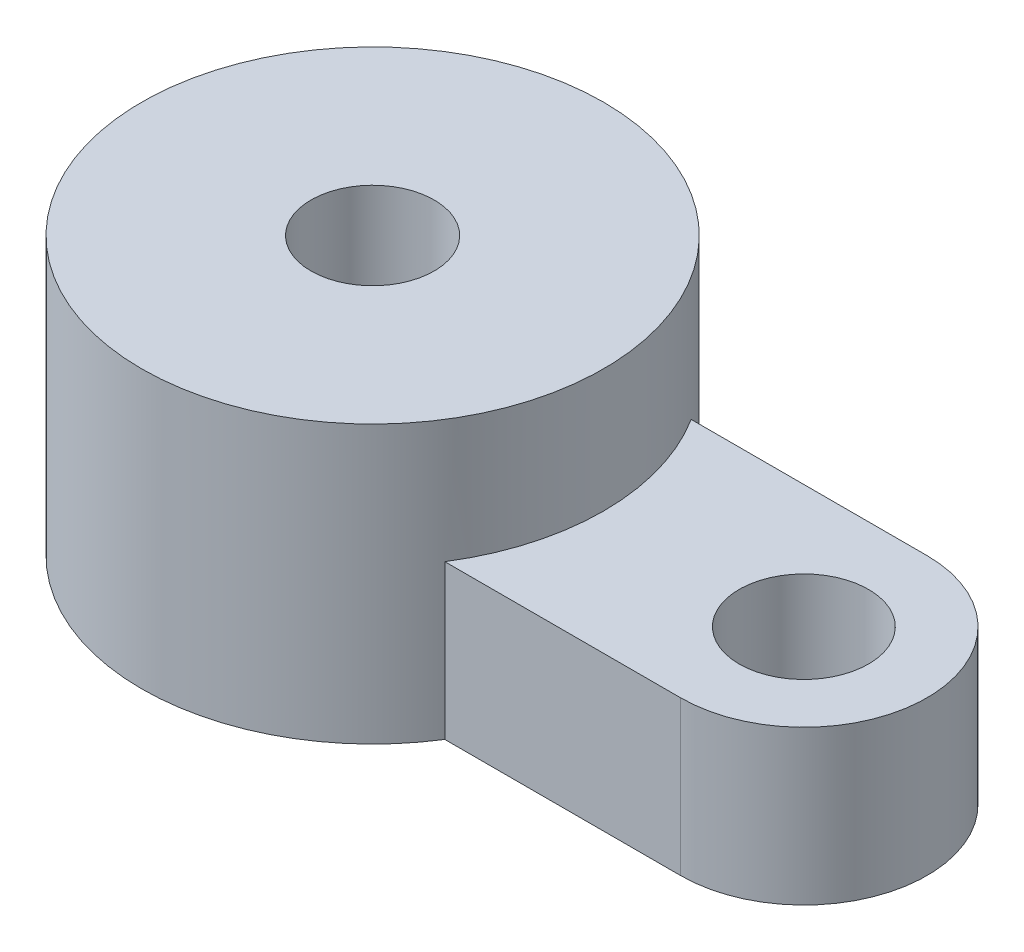
SolidWorks part; units mm, degrees
ref_plane "前视基准面" through (0, 0, 0) normal (0, 0, 1) x (1, 0, 0)
ref_plane "上视基准面" through (0, 0, 0) normal (0, 1, 0) x (1, 0, 0)
ref_plane "右视基准面" through (0, 0, 0) normal (1, 0, 0) x (0, 0, -1)
sketch "草图1" plane through (0, 0, 0) normal (0, 1, 0) x (1, 0, 0)
  line L0 (0, 0) -> (14.003, 0) construction
  line L1 (0, 4) -> (14.003, 4)
  line L2 (0, -4) -> (14.003, -4)
  arc A0 (0, 4) -> (0, -4) centre (0, 0) ccw
  arc A1 (14.003, -4) -> (14.003, 4) centre (14.003, 0) ccw
  circle A2 centre (0, 0) radius 2.1
  circle A3 centre (14.003, 0) radius 2.1
  point P3 (7.0015, 0)
  dimension "D1" = 14.003
  dimension "D2" = 4.2
  dimension "D3" = 4.2
  dimension "D4" = 4
extrude "凸台-拉伸1" add sketch "草图1" along normal blind 5 contours A2
sketch "草图2" plane through (0, 5, 0) normal (0, 1, 0) x (1, 0, 0)
  circle A0 centre (0, 0) radius 7.5
  circle A1 centre (0, 0) radius 2
  dimension "D1" = 15
  dimension "D2" = 4
extrude "凸台-拉伸2" add sketch "草图2" along normal blind 4 and the other way blind 5
sketch "草图3" plane through (0, 0, 0) normal (0, 0, 1) x (1, 0, 0)
  line L0 (0, 0) -> (0, 9) construction
  line L1 (2, 9) -> (-2, 9) construction
  circle A0 centre (0, 4.5) radius 1.85
  dimension "D1" = 3.7
extrude "切除-拉伸1" cut sketch "草图3" against normal blind 12
